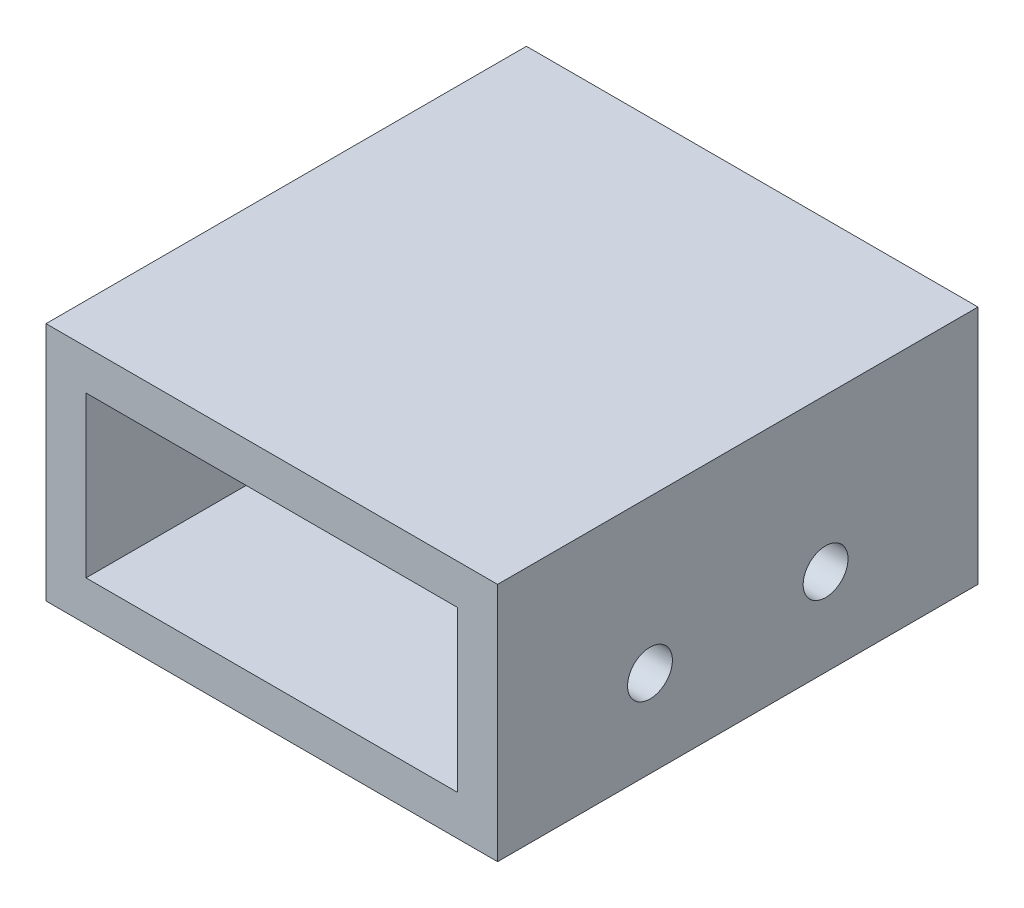
SolidWorks part; units mm, degrees
ref_plane "Front Plane" through (0, 0, 0) normal (0, 0, 1) x (1, 0, 0)
ref_plane "Top Plane" through (0, 0, 0) normal (0, 1, 0) x (1, 0, 0)
ref_plane "Right Plane" through (0, 0, 0) normal (1, 0, 0) x (0, 0, -1)
sketch "Sketch1" plane through (0, 0, 0) normal (0, 0, 1) x (1, 0, 0)
  line L0 (0, 0) -> (0, 19.05)
  line L1 (0, 19.05) -> (-35.814, 19.05)
  line L2 (-35.814, 19.05) -> (-35.814, 0)
  line L3 (-35.814, 0) -> (-21.209, 0)
  line L4 (-21.209, 0) -> (-21.209, 3.175)
  line L5 (-21.209, 3.175) -> (-32.639, 3.175)
  line L6 (-32.639, 3.175) -> (-32.639, 15.875)
  line L7 (-32.639, 15.875) -> (-3.175, 15.875)
  line L8 (-3.175, 15.875) -> (-3.175, 0)
  line L9 (-3.175, 0) -> (0, 0)
  dimension "D1" = 35.814
  dimension "D2" = 19.05
  dimension "D3" = 3.175
  dimension "D4" = 3.175
  dimension "D5" = 3.175
  dimension "D6" = 3.175
  dimension "D7" = 11.43
extrude "Boss-Extrude1" add sketch "Sketch1" against normal blind 38.1
sketch "Sketch2" plane through (0, 0, 0) normal (1, 0, 0) x (0, 0, -1)
  line L0 (38.1, 0) -> (38.1, 19.05) construction
  line L1 (0, 0) -> (0, 19.05) construction
  line L2 (38.1, 0) -> (0, 0) construction
  circle A0 centre (26.0141, 6.9139) radius 1.778
  circle A1 centre (12.0859, 6.9139) radius 1.778
  dimension "D2" = 3.556
  dimension "D4" = 3.556
  dimension "D1" = 12.0859
  dimension "D3" = 12.0859
  dimension "D5" = 6.9139
  dimension "D6" = 6.9139
extrude "Cut-Extrude1" cut sketch "Sketch2" against normal blind 15.24 contours A1 | A0
sketch "Sketch4" plane through (0, 0, 0) normal (0, 0, 1) x (1, 0, 0)
  line L1 (-3.175, 0) -> (-21.209, 0)
  line L2 (-3.175, 0) -> (-3.175, 3.175)
  line L3 (-3.175, 3.175) -> (-21.209, 3.175)
  line L4 (-21.209, 0) -> (-21.209, 3.175)
extrude "Boss-Extrude2" add sketch "Sketch4" against normal blind 38.1
sketch "Sketch3" plane through (0, 0, 0) normal (0, -1, 0) x (-1, 0, 0)
  line L0 (35.814, 38.1) -> (0, 38.1) construction
  line L1 (35.814, 38.1) -> (35.814, 0) construction
  circle A0 centre (26.543, 19.05) radius 1.778
  circle A1 centre (7.747, 19.05) radius 1.778
  point P8 (0, 0)
  dimension "D3" = 3.556
  dimension "D4" = 3.556
  dimension "D1" = 19.05
  dimension "D2" = 9.271
  dimension "D5" = 18.796
extrude "Cut-Extrude2" cut sketch "Sketch3" against normal blind 15.24
